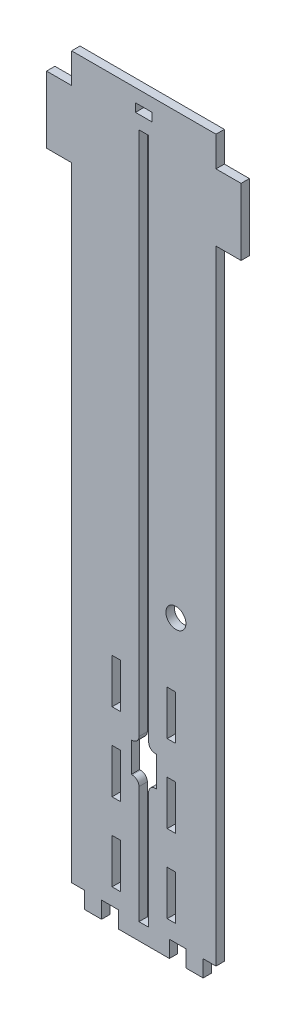
SolidWorks part; units mm, degrees
material "Acrylic (Medium-high impact)"
ref_plane "Front" through (0, 0, 0) normal (0, 0, 1) x (1, 0, 0)
ref_plane "Top" through (0, 0, 0) normal (0, 1, 0) x (1, 0, 0)
ref_plane "Right" through (0, 0, 0) normal (1, 0, 0) x (0, 0, -1)
sketch "Sketch1" plane through (0, 0, 0) normal (0, 0, 1) x (1, 0, 0)
  line L0 (0, 130.302) -> (0, -130.302) construction
  line L1 (-1.8415, 130.302) -> (-1.8415, -130.302)
  line L2 (-1.8415, -130.302) -> (1.8415, -130.302)
  line L3 (1.8415, 130.302) -> (1.8415, -130.302)
  line L4 (1.8415, 130.302) -> (-1.8415, 130.302)
  line L8 (-27.432, 143.51) -> (27.432, 143.51)
  line L9 (-27.432, 143.51) -> (-27.432, -136.652)
  line L10 (-27.432, -136.652) -> (27.432, -136.652)
  line L11 (27.432, 143.51) -> (27.432, -136.652)
  point P2 (0, -130.302)
  point P7 (0, 143.51)
  point P11 (0, 0)
  dimension "D1" = 3.683
  dimension "D4" = 260.604
  dimension "D7" = 6.35
  dimension "D2" = 54.864
  dimension "D3" = 273.812
extrude "Boss-Extrude1" add sketch "Sketch1" along normal blind 3.175
sketch "Sketch2" plane through (27.432, 0, 0) normal (1, 0, 0) x (0, 0, -1)
  line L0 (-3.175, -136.652) -> (-3.175, 143.51) construction
  line L1 (-3.175, -35.052) -> (228.6, -35.052)
  line L2 (-3.175, -35.052) -> (-3.175, -136.652)
  line L3 (-3.175, -136.652) -> (228.6, -136.652)
  line L4 (228.6, -35.052) -> (228.6, -136.652)
  line L5 (14.4, -88.392) -> (14.4, -83.312)
  line L6 (36.4, -83.312) -> (36.4, -88.392)
  line L7 (8.4, -103.892) -> (8.4, -98.812)
  line L8 (11.4, -103.892) -> (11.4, -98.812)
  line L9 (8.4, -72.892) -> (8.4, -67.812)
  line L10 (11.4, -72.892) -> (11.4, -67.812)
  line L11 (25.4, -83.312) -> (25.4, -88.392) construction
  line L12 (42.4, -103.892) -> (42.4, -98.812)
  line L13 (39.4, -103.892) -> (39.4, -98.812)
  line L14 (39.4, -72.892) -> (39.4, -67.812)
  line L15 (42.4, -72.892) -> (42.4, -67.812)
  line L16 (0, -136.652) -> (0, 143.51) construction
  line L17 (227.0125, -47.752) -> (227.0125, -64.6853) construction
  line L18 (228.6, -35.052) -> (225.425, -35.052)
  line L19 (228.6, -35.052) -> (228.6, -47.752)
  line L20 (228.6, -47.752) -> (225.425, -47.752)
  line L21 (225.425, -35.052) -> (225.425, -47.752)
  line L22 (228.6, -94.3187) -> (225.425, -94.3187)
  line L23 (228.6, -94.3187) -> (228.6, -107.0187)
  line L24 (228.6, -107.0187) -> (225.425, -107.0187)
  line L25 (225.425, -94.3187) -> (225.425, -107.0187)
  line L26 (228.6, -123.952) -> (225.425, -123.952)
  line L27 (228.6, -123.952) -> (228.6, -136.652)
  line L28 (228.6, -136.652) -> (225.425, -136.652)
  line L29 (225.425, -123.952) -> (225.425, -136.652)
  line L30 (228.6, -64.6853) -> (225.425, -64.6853)
  line L31 (228.6, -64.6853) -> (228.6, -77.3853)
  line L32 (228.6, -77.3853) -> (225.425, -77.3853)
  line L33 (225.425, -64.6853) -> (225.425, -77.3853)
  line L34 (227.0125, -77.3853) -> (227.0125, -94.3187) construction
  line L35 (227.0125, -107.0187) -> (227.0125, -123.952) construction
  arc A0 (14.4, -88.392) -> (36.4, -88.392) centre (25.4, -88.392) ccw
  arc A1 (36.4, -83.312) -> (14.4, -83.312) centre (25.4, -83.312) ccw
  arc A2 (8.4, -103.892) -> (11.4, -103.892) centre (9.9, -103.892) ccw
  arc A3 (11.4, -98.812) -> (8.4, -98.812) centre (9.9, -98.812) ccw
  arc A4 (8.4, -72.892) -> (11.4, -72.892) centre (9.9, -72.892) ccw
  arc A5 (11.4, -67.812) -> (8.4, -67.812) centre (9.9, -67.812) ccw
  arc A6 (42.4, -103.892) -> (39.4, -103.892) centre (40.9, -103.892) cw
  arc A7 (39.4, -98.812) -> (42.4, -98.812) centre (40.9, -98.812) cw
  arc A8 (42.4, -72.892) -> (39.4, -72.892) centre (40.9, -72.892) cw
  arc A9 (39.4, -67.812) -> (42.4, -67.812) centre (40.9, -67.812) cw
  point P44 (25.4, -85.852)
  point P47 (-3.175, -85.852)
  line M17 (0, -136.652) -> (0, 143.51)
  line M19 (-3.175, 143.51) -> (-3.175, -136.652)
  line M20 (-3.175, -136.652) -> (0, -136.652)
  dimension "D1" = 22
  dimension "D6" = 1.5
  dimension "D10" = 1.5
  dimension "D2" = 5.08
  dimension "D3" = 5.08
  dimension "D4" = 15.5
  dimension "D5" = 15.5
  dimension "D7" = 15.5
  dimension "D8" = 15.5
  dimension "D9" = 5.08
  dimension "D11" = 25.4
  dimension "D12" = 50.8
  dimension "D13" = 203.2
  dimension "D14" = 12.7
  dimension "D15" = 3.175
extrude "Boss-Extrude2" add sketch "Sketch2" against normal blind 3.175 contours L33 L30 L4 L20 L21 L1 L3 L29 L26 L24 L25 L22 L32 A5 L10 A4 L9 A3 L8 A2 L7 A1 L6 A0 L5 L13 A7 L12 A6 L14 A9 L15 A8 M17 | L1 M19 M20 M17
sketch "Sketch3" plane through (24.257, 0, 0) normal (-1, 0, 0) x (0, 0, 1)
  line L0 (-225.425, -123.952) -> (-225.425, -136.652) construction
  line L1 (-225.425, -130.302) -> (0, -130.302)
  line L2 (-225.425, -130.302) -> (-225.425, -136.652)
  line L3 (-225.425, -136.652) -> (0, -136.652)
  line L4 (0, -130.302) -> (0, -136.652)
  dimension "D1" = 6.35
extrude "Boss-Extrude3" add sketch "Sketch3" along normal up to surface (51.689 mm away) up to face at (-27.432, 3.429, 1.5875)
sketch "Sketch4" plane through (0, -136.652, 0) normal (0, -1, 0) x (1, 0, 0)
  line L0 (22.5425, -23.8125) -> (22.5425, -36.5125)
  line L1 (27.432, 3.175) -> (22.5425, 3.175)
  line L2 (27.432, 3.175) -> (27.432, -9.525)
  line L3 (27.432, -9.525) -> (22.5425, -9.525)
  line L4 (22.5425, 3.175) -> (22.5425, -9.525)
  line L5 (27.432, -23.8125) -> (22.5425, -23.8125)
  line L6 (27.432, -23.8125) -> (27.432, -36.5125)
  line L7 (27.432, -36.5125) -> (22.5425, -36.5125)
  line L8 (22.5425, -50.8) -> (22.5425, -63.5)
  line L9 (27.432, -50.8) -> (22.5425, -50.8)
  line L10 (27.432, -50.8) -> (27.432, -63.5)
  line L11 (27.432, -63.5) -> (22.5425, -63.5)
  line L12 (22.5425, -77.7875) -> (22.5425, -90.4875)
  line L13 (27.432, -77.7875) -> (22.5425, -77.7875)
  line L14 (27.432, -77.7875) -> (27.432, -90.4875)
  line L15 (27.432, -90.4875) -> (22.5425, -90.4875)
  line L16 (22.5425, -104.775) -> (22.5425, -117.475)
  line L17 (27.432, -104.775) -> (22.5425, -104.775)
  line L18 (27.432, -104.775) -> (27.432, -117.475)
  line L19 (27.432, -117.475) -> (22.5425, -117.475)
  line L20 (22.5425, -131.7625) -> (22.5425, -144.4625)
  line L21 (27.432, -131.7625) -> (22.5425, -131.7625)
  line L22 (27.432, -131.7625) -> (27.432, -144.4625)
  line L23 (27.432, -144.4625) -> (22.5425, -144.4625)
  line L24 (22.5425, -158.75) -> (22.5425, -171.45)
  line L25 (27.432, -158.75) -> (22.5425, -158.75)
  line L26 (27.432, -158.75) -> (27.432, -171.45)
  line L27 (27.432, -171.45) -> (22.5425, -171.45)
  line L28 (22.5425, -185.7375) -> (22.5425, -198.4375)
  line L29 (27.432, -185.7375) -> (22.5425, -185.7375)
  line L30 (27.432, -185.7375) -> (27.432, -198.4375)
  line L31 (27.432, -198.4375) -> (22.5425, -198.4375)
  line L32 (22.5425, -212.725) -> (22.5425, -225.425)
  line L33 (27.432, -212.725) -> (22.5425, -212.725)
  line L34 (27.432, -212.725) -> (27.432, -225.425)
  line L35 (27.432, -225.425) -> (22.5425, -225.425)
  line L36 (0, 3.175) -> (0, -225.425) construction
  line L37 (-27.432, 3.175) -> (27.432, 3.175) construction
  line L38 (-27.432, -225.425) -> (27.432, -225.425) construction
  line L39 (-22.5425, 3.175) -> (-22.5425, -225.425)
  line L40 (27.432, 3.175) -> (22.5425, 3.175)
  line L41 (27.432, 3.175) -> (27.432, -225.425)
  line L42 (27.432, -225.425) -> (22.5425, -225.425)
  line L43 (22.5425, 3.175) -> (22.5425, -225.425)
  line L44 (-27.432, -225.425) -> (-22.5425, -225.425)
  line L45 (-27.432, 3.175) -> (-27.432, -225.425)
  line L46 (-27.432, 3.175) -> (-22.5425, 3.175)
  line L47 (-27.432, -225.425) -> (-22.5425, -225.425)
  line L48 (-27.432, -212.725) -> (-27.432, -225.425)
  line L49 (-27.432, -212.725) -> (-22.5425, -212.725)
  line L50 (-22.5425, -212.725) -> (-22.5425, -225.425)
  line L51 (-27.432, -198.4375) -> (-22.5425, -198.4375)
  line L52 (-27.432, -185.7375) -> (-27.432, -198.4375)
  line L53 (-27.432, -185.7375) -> (-22.5425, -185.7375)
  line L54 (-22.5425, -185.7375) -> (-22.5425, -198.4375)
  line L55 (-27.432, -171.45) -> (-22.5425, -171.45)
  line L56 (-27.432, -158.75) -> (-27.432, -171.45)
  line L57 (-27.432, -158.75) -> (-22.5425, -158.75)
  line L58 (-22.5425, -158.75) -> (-22.5425, -171.45)
  line L59 (-27.432, -144.4625) -> (-22.5425, -144.4625)
  line L60 (-27.432, -131.7625) -> (-27.432, -144.4625)
  line L61 (-27.432, -131.7625) -> (-22.5425, -131.7625)
  line L62 (-22.5425, -131.7625) -> (-22.5425, -144.4625)
  line L63 (-27.432, -117.475) -> (-22.5425, -117.475)
  line L64 (-27.432, -104.775) -> (-27.432, -117.475)
  line L65 (-27.432, -104.775) -> (-22.5425, -104.775)
  line L66 (-22.5425, -104.775) -> (-22.5425, -117.475)
  line L67 (-27.432, -90.4875) -> (-22.5425, -90.4875)
  line L68 (-27.432, -77.7875) -> (-27.432, -90.4875)
  line L69 (-27.432, -77.7875) -> (-22.5425, -77.7875)
  line L70 (-22.5425, -77.7875) -> (-22.5425, -90.4875)
  line L71 (-27.432, -63.5) -> (-22.5425, -63.5)
  line L72 (-27.432, -50.8) -> (-27.432, -63.5)
  line L73 (-27.432, -50.8) -> (-22.5425, -50.8)
  line L74 (-22.5425, -50.8) -> (-22.5425, -63.5)
  line L75 (-27.432, -36.5125) -> (-22.5425, -36.5125)
  line L76 (-27.432, -23.8125) -> (-27.432, -36.5125)
  line L77 (-27.432, -23.8125) -> (-22.5425, -23.8125)
  line L78 (-22.5425, 3.175) -> (-22.5425, -9.525)
  line L79 (-27.432, -9.525) -> (-22.5425, -9.525)
  line L80 (-27.432, 3.175) -> (-27.432, -9.525)
  line L81 (-27.432, 3.175) -> (-22.5425, 3.175)
  line L82 (-22.5425, -23.8125) -> (-22.5425, -36.5125)
  line L83 (-9.7155, 1.5875) -> (9.7155, 1.5875) construction
  line L85 (-27.432, 3.175) -> (-22.1615, 3.175)
  line L86 (-27.432, 3.175) -> (-27.432, 0)
  line L87 (-27.432, 0) -> (-22.1615, 0)
  line L88 (-22.1615, 3.175) -> (-22.1615, 0)
  line L92 (22.1615, 3.175) -> (22.1615, 0)
  line L93 (22.1615, 3.175) -> (27.432, 3.175)
  line L94 (27.432, 3.175) -> (27.432, 0)
  line L95 (22.1615, 0) -> (27.432, 0)
  line L96 (-27.432, 3.175) -> (27.432, 3.175)
  line L97 (-27.432, 3.175) -> (-27.432, 0)
  line L98 (-27.432, 0) -> (27.432, 0)
  line L99 (27.432, 3.175) -> (27.432, 0)
  line L100 (-2.6353, 3.175) -> (-2.6352, 0) [skipped]
  line L101 (-2.6352, 0) -> (2.6352, 0) [skipped]
  line L102 (2.6353, 3.175) -> (2.6352, 0) [skipped]
  line L103 (-2.6353, 3.175) -> (2.6353, 3.175) [skipped]
  line L104 (-9.7155, 0) -> (-16.0655, 0)
  line L105 (-9.7155, 0) -> (-9.7155, 3.175)
  line L106 (-9.7155, 3.175) -> (-16.0655, 3.175)
  line L107 (-16.0655, 0) -> (-16.0655, 3.175)
  line L111 (9.7155, 3.175) -> (16.0655, 3.175)
  line L112 (9.7155, 3.175) -> (9.7155, 0)
  line L113 (9.7155, 0) -> (16.0655, 0)
  line L114 (16.0655, 3.175) -> (16.0655, 0)
  point P86 (0, 1.5875)
  line M39 (27.432, 3.175) -> (-27.432, 3.175)
  line M40 (-27.432, 3.175) -> (-27.432, -225.425)
  dimension "D7" = 6.35
  dimension "D2" = 12.7
  dimension "D4" = 3.175
  dimension "D8" = 6.35
  dimension "D1" = 6.477
  dimension "D5" = 19.431
  dimension "D9" = 6.096
  dimension "D3" = 9
  dimension "D6" = 3
sketch "Sketch6" plane through (0, 0, 3.175) normal (0, 0, 1) x (1, 0, 0)
  line L1 (27.432, -47.752) -> (24.257, -47.752)
  line L2 (27.432, -47.752) -> (27.432, -64.6853)
  line L3 (27.432, -64.6853) -> (24.257, -64.6853)
  line L4 (24.257, -47.752) -> (24.257, -64.6853)
  line L5 (27.432, -77.3853) -> (24.257, -77.3853)
  line L6 (27.432, -77.3853) -> (27.432, -94.3187)
  line L7 (27.432, -94.3187) -> (24.257, -94.3187)
  line L8 (24.257, -77.3853) -> (24.257, -94.3187)
  line L9 (27.432, -107.0187) -> (24.257, -107.0187)
  line L10 (27.432, -107.0187) -> (27.432, -123.952)
  line L11 (27.432, -123.952) -> (24.257, -123.952)
  line L12 (24.257, -107.0187) -> (24.257, -123.952)
sketch "Sketch7" plane through (27.432, 0, 0) normal (1, 0, 0) x (0, 0, -1)
  line L0 (0, -35.052) -> (0, 143.51) construction
  line L1 (0, -8.6302) -> (327.0227, -8.6302)
  line L2 (0, -8.6302) -> (0, -288.0659)
  line L3 (0, -288.0659) -> (327.0227, -288.0659)
  line L4 (327.0227, -8.6302) -> (327.0227, -288.0659)
extrude "Cut-Extrude1" cut sketch "Sketch7" against normal through all
extrude "Cut-Extrude2" cut sketch "Sketch4" against normal blind 6.35 contours L107 L98 L105 L96 | L4 L95 L41 M39 | L87 L39 M40 M39 | L114 L96 L112 L98 | L20 L23 L22 L21 | L10 L11 L8 L9 | L24 L27 L26 L25
extrude "Cut-Extrude3" [suppressed] cut sketch "Sketch6" against normal through all
sketch "Sketch8" plane through (0, 0, 3.175) normal (0, 0, 1) x (1, 0, 0)
  line L0 (-27.432, 143.51) -> (-27.432, -130.302) construction
  line L1 (-27.432, 132.08) -> (-36.957, 132.08)
  line L2 (-27.432, 132.08) -> (-27.432, 106.68)
  line L3 (-27.432, 106.68) -> (-36.957, 106.68)
  line L4 (-36.957, 132.08) -> (-36.957, 106.68)
  line L5 (27.432, -130.302) -> (27.432, 143.51) construction
  line L6 (27.432, 132.08) -> (36.957, 132.08)
  line L7 (27.432, 132.08) -> (27.432, 106.68)
  line L8 (27.432, 106.68) -> (36.957, 106.68)
  line L9 (36.957, 132.08) -> (36.957, 106.68)
  line L10 (27.432, 143.51) -> (-27.432, 143.51) construction
  dimension "D1" = 9.525
  dimension "D2" = 25.4
  dimension "D3" = 11.43
extrude "Boss-Extrude4" add sketch "Sketch8" against normal up to surface (3.175 mm away) up to face at (0, 0, 0)
sketch "Sketch9" plane through (0, 0, 3.175) normal (0, 0, 1) x (1, 0, 0)
  line L0 (-8.89, -56.2187) -> (8.89, -56.2187) construction
  line L1 (-12.065, -47.752) -> (-8.89, -47.752)
  line L2 (-12.065, -47.752) -> (-12.065, -64.6853)
  line L3 (-12.065, -64.6853) -> (-8.89, -64.6853)
  line L4 (-8.89, -47.752) -> (-8.89, -64.6853)
  line L6 (-12.065, -77.3853) -> (-8.89, -77.3853)
  line L7 (-12.065, -77.3853) -> (-12.065, -94.3187)
  line L8 (-12.065, -94.3187) -> (-8.89, -94.3187)
  line L9 (-8.89, -77.3853) -> (-8.89, -94.3187)
  line L10 (-12.065, -107.0187) -> (-8.89, -107.0187)
  line L11 (-12.065, -107.0187) -> (-12.065, -123.952)
  line L12 (-12.065, -123.952) -> (-8.89, -123.952)
  line L13 (-8.89, -107.0187) -> (-8.89, -123.952)
  line L14 (8.89, -47.752) -> (12.065, -47.752)
  line L15 (8.89, -47.752) -> (8.89, -64.6853)
  line L16 (8.89, -64.6853) -> (12.065, -64.6853)
  line L18 (27.432, -47.752) -> (24.257, -47.752) construction
  line L19 (24.257, -47.752) -> (24.257, -64.6853) construction
  line L20 (-1.8415, -130.302) -> (1.8415, -130.302) construction
  line L21 (12.065, -47.752) -> (12.065, -64.6853)
  line L22 (8.89, -77.3853) -> (12.065, -77.3853)
  line L23 (8.89, -77.3853) -> (8.89, -94.3187)
  line L24 (8.89, -94.3187) -> (12.065, -94.3187)
  line L25 (12.065, -77.3853) -> (12.065, -94.3187)
  line L26 (8.89, -107.0187) -> (12.065, -107.0187)
  line L27 (8.89, -107.0187) -> (8.89, -123.952)
  line L28 (8.89, -123.952) -> (12.065, -123.952)
  line L29 (12.065, -107.0187) -> (12.065, -123.952)
  line L31 (-22.5425, -130.302) -> (-27.432, -130.302) construction
  line L32 (-10.4775, -94.3187) -> (-10.4775, -107.0187) construction
  line L33 (-10.4775, -77.3853) -> (-10.4775, -64.6853) construction
  point P26 (0, -56.2187)
  point P36 (0, -130.302)
  dimension "D1" = 17.78
  dimension "D3" = 6.35
  dimension "D4" = 12.7
extrude "Cut-Extrude4" cut sketch "Sketch9" against normal through all
sketch "Sketch10" plane through (0, 0, 3.175) normal (0, 0, 1) x (1, 0, 0)
  line L0 (-27.432, 132.08) -> (-36.957, 132.08) construction
  line L1 (-3.175, 138.557) -> (3.175, 138.557)
  line L2 (-3.175, 138.557) -> (-3.175, 135.382)
  line L3 (-3.175, 135.382) -> (3.175, 135.382)
  line L4 (3.175, 138.557) -> (3.175, 135.382)
  line L5 (27.432, 143.51) -> (-27.432, 143.51) construction
  point P6 (0, 135.382)
  point P9 (0, 143.51)
  dimension "D1" = 3.302
  dimension "D2" = 6.35
  dimension "D3" = 3.175
extrude "Cut-Extrude5" cut sketch "Sketch10" against normal through all
sketch "Sketch11" plane through (0, 0, 3.175) normal (0, 0, 1) x (1, 0, 0)
  line L0 (27.432, -130.302) -> (22.5425, -130.302) construction
  line L1 (-2.8575, -71.882) -> (2.8575, -71.882)
  line L2 (-2.8575, -71.882) -> (-2.8575, -79.502)
  line L3 (-2.8575, -79.502) -> (2.8575, -79.502)
  line L4 (2.8575, -71.882) -> (2.8575, -79.502)
  line L5 (-1.8415, -130.302) -> (1.8415, -130.302) construction
  point P9 (0, -71.882)
  point P12 (0, -130.302)
  dimension "D1" = 7.62
  dimension "D2" = 50.8
  dimension "D3" = 5.715
extrude "Cut-Extrude6" [suppressed] cut sketch "Sketch11" against normal through all
sketch "Sketch12" plane through (0, 0, 3.175) normal (0, 0, 1) x (1, 0, 0)
  line L0 (-22.5425, -130.302) -> (-27.432, -130.302) construction
  line L1 (-22.5425, -136.652) -> (-16.0655, -136.652)
  line L2 (-22.5425, -136.652) -> (-22.5425, -137.16)
  line L3 (-22.5425, -137.16) -> (-16.0655, -137.16)
  line L4 (-16.0655, -136.652) -> (-16.0655, -137.16)
  line L5 (-9.7155, -136.652) -> (9.7155, -136.652)
  line L6 (-9.7155, -136.652) -> (-9.7155, -137.16)
  line L7 (-9.7155, -137.16) -> (9.7155, -137.16)
  line L8 (22.5425, -136.652) -> (22.5425, -137.16)
  line L9 (16.0655, -130.302) -> (16.0655, -136.652) construction
  line L11 (9.7155, -136.652) -> (9.7155, -137.16)
  line L13 (16.0655, -136.652) -> (16.0655, -137.16)
  line L14 (16.0655, -136.652) -> (22.5425, -136.652)
  line L15 (16.0655, -137.16) -> (22.5425, -137.16)
  dimension "D1" = 6.858
extrude "Boss-Extrude5" [suppressed] add sketch "Sketch12" against normal up to surface (2.9972 mm away)
sketch "Sketch13" plane through (0, 0, 3.175) normal (0, 0, 1) x (1, 0, 0)
  line L0 (-9.7155, -136.652) -> (9.7155, -136.652) construction
  line L1 (-4.7625, -71.882) -> (4.7625, -71.882)
  line L2 (-4.7625, -71.882) -> (-4.7625, -83.312)
  line L3 (-4.7625, -83.312) -> (4.7625, -83.312)
  line L4 (4.7625, -71.882) -> (4.7625, -83.312)
  line L5 (-1.8415, -130.302) -> (1.8415, -130.302) construction
  point P10 (0, -71.882)
  point P13 (0, -130.302)
  dimension "D1" = 53.34
  dimension "D2" = 64.77
  dimension "D3" = 9.525
extrude "Cut-Extrude7" cut sketch "Sketch13" against normal through all
sketch "Sketch14" plane through (0, 0, 3.175) normal (0, 0, 1) x (1, 0, 0)
  line L0 (16.0655, -130.302) -> (9.7155, -130.302) construction
  line L1 (27.432, -130.302) -> (27.432, 106.68) construction
  circle A0 centre (12.192, -23.3172) radius 3.81
  dimension "D3" = 7.62
  dimension "D1" = 106.9848
  dimension "D2" = 15.24
extrude "Cut-Extrude8" cut sketch "Sketch14" against normal through all
fillet "Fillet1" radius 2.54 4 edges at (1.8415, -71.882, 1.5875) (-1.8415, -71.882, 1.5875) (1.8415, -83.312, 1.5875) (-1.8415, -83.312, 1.5875)
sketch "Sketch15" plane through (0, 0, 3.175) normal (0, 0, 1) x (1, 0, 0)
  line L0 (-36.957, 132.08) -> (-36.957, 106.68) construction
  line L1 (-36.957, 143.51) -> (36.957, 143.51)
  line L2 (-36.957, 143.51) -> (-36.957, -21.7794)
  line L3 (-36.957, -21.7794) -> (36.957, -21.7794)
  line L4 (36.957, 143.51) -> (36.957, -21.7794)
  line L5 (36.957, 106.68) -> (36.957, 132.08) construction
extrude "Cut-Extrude9" [suppressed] cut sketch "Sketch15" against normal through all
equation "\"bottomThickness\"= .25in"
equation "\"wallThickness\"= .125in"
equation "\"D7@Sketch1\"=\"bottomThickness\""
equation "\"D1@Boss-Extrude1\"=\"wallThickness\""
equation "\"D15@Sketch2\"=\"wallThickness\""
equation "\"D1@Boss-Extrude2\"=\"wallThickness\""
equation "\"D1@Sketch3\"=\"bottomThickness\""
equation "\"D4@Sketch4\"=\"wallThickness\""
equation "\"D1@Sketch10\"=\"wallThickness\"+.005"
equation "\"D1@Cut-Extrude2\"=\"bottomThickness\""
equation "\"D1@Sketch12\"=\"bottomThickness\"+.02"
